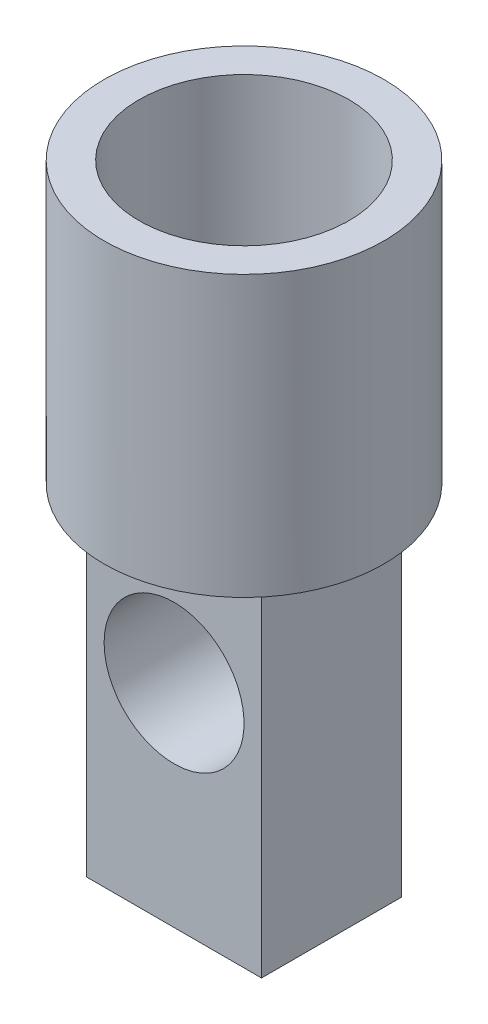
SolidWorks part; units mm, degrees
ref_plane "Front Plane" through (0, 0, 0) normal (0, 0, 1) x (1, 0, 0)
ref_plane "Top Plane" through (0, 0, 0) normal (0, 1, 0) x (1, 0, 0)
ref_plane "Right Plane" through (0, 0, 0) normal (1, 0, 0) x (0, 0, -1)
sketch "Sketch1" plane through (0, 0, 0) normal (0, 0, 1) x (1, 0, 0)
  line L0 (-2, 0) -> (-2, 3)
  line L1 (-2, 3) -> (-1.5, 3)
  line L2 (-1.5, 3) -> (-1.5, 0)
  line L3 (-1.5, 0) -> (-2, 0)
  line L4 (0, 0) -> (0, 39.2659) construction
  point P5 (0, 0)
  dimension "D1" = 3
  dimension "D2" = 3
  dimension "D3" = 0.5
revolve "Revolve1" add sketch "Sketch1" angle 360 about L4
sketch "Sketch2" plane through (0, 0, 0) normal (0, 1, 0) x (1, 0, 0)
  circle A0 centre (0, 0) radius 2 construction
  circle A1 centre (0, 0) radius 2
extrude "Boss-Extrude1" add sketch "Sketch2" against normal blind 1
sketch "Sketch3" plane through (0, -1, 0) normal (0, -1, 0) x (1, 0, 0)
  line L1 (-1.25, -1) -> (1.25, -1)
  line L2 (-1.25, -1) -> (-1.25, 1)
  line L3 (-1.25, 1) -> (1.25, 1)
  line L4 (1.25, -1) -> (1.25, 1)
  line L5 (-1.25, -1) -> (1.25, 1) construction
  line L6 (-1.25, 1) -> (1.25, -1) construction
  point P0 (0, 0)
  dimension "D1" = 2
  dimension "D2" = 2.5
extrude "Boss-Extrude2" add sketch "Sketch3" along normal blind 5
sketch "Sketch4" plane through (0, 0, 0) normal (0, 0, -1) x (-1, 0, 0)
  circle A0 centre (0, -2.9731) radius 1
  point P2 (0, 0)
  point P4 (0, -2.9731)
  dimension "D1" = 2
extrude "Cut-Extrude1" cut sketch "Sketch4" against normal through all both and the other way through all
